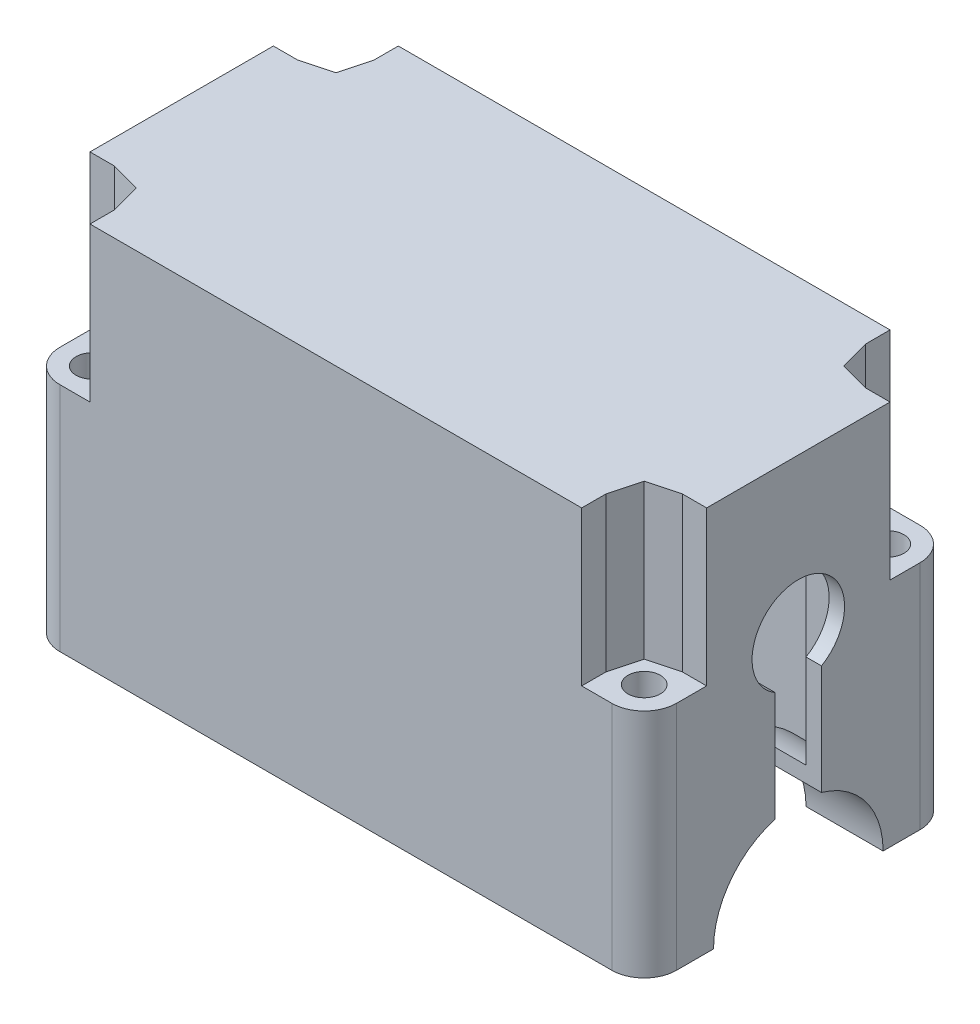
SolidWorks part; units mm, degrees
ref_plane "Front Plane" through (0, 0, 0) normal (0, 0, 1) x (1, 0, 0)
ref_plane "Top Plane" through (0, 0, 0) normal (0, 1, 0) x (1, 0, 0)
ref_plane "Right Plane" through (0, 0, 0) normal (1, 0, 0) x (0, 0, -1)
sketch "Esquisse1" plane through (0, 0, 0) normal (0, 1, 0) x (1, 0, 0)
  line L1 (0, 0) -> (80, 0)
  line L2 (0, 0) -> (0, 40)
  line L3 (0, 40) -> (80, 40)
  line L4 (80, 0) -> (80, 40)
  dimension "D1" = 40
  dimension "D2" = 80
extrude "Boss.-Extru.1" add sketch "Esquisse1" along normal blind 50
sketch "Esquisse2" plane through (0, 0, 0) normal (-1, 0, 0) x (0, 0, 1)
  line L0 (-40, 0) -> (0, 0) construction
  line L1 (-38, 48) -> (-2, 48)
  line L2 (-38, 48) -> (-38, 2)
  line L3 (-38, 2) -> (-2, 2)
  line L4 (-2, 48) -> (-2, 2)
  line L5 (-40, 50) -> (-40, 0) construction
  line L6 (-40, 50) -> (0, 50) construction
  line L7 (0, 50) -> (0, 0) construction
  circle A0 centre (-20, 0) radius 13
  dimension "D1" = 26
  dimension "D2" = 2
  dimension "D3" = 2
  dimension "D4" = 2
  dimension "D5" = 2
extrude "Enlèv. mat.-Extru.1" cut sketch "Esquisse2" against normal blind 78 contours A0 L3 L4 L1 L2
sketch "Esquisse3" plane through (0, 0, -40) normal (0, 0, -1) x (-1, 0, 0)
  line L0 (-80, 0) -> (0, 0) construction
  line L1 (0, 50) -> (-2, 50)
  line L2 (0, 50) -> (0, 0)
  line L3 (0, 0) -> (-2, 0)
  line L4 (-2, 50) -> (-2, 0)
  dimension "D1" = 2
extrude "Boss.-Extru.2" add sketch "Esquisse3" against normal blind 40
sketch "Esquisse4" plane through (0, 0, 0) normal (-1, 0, 0) x (0, 0, 1)
  line L0 (-40, 0) -> (0, 0) construction
  circle A0 centre (-20, 0) radius 11
  dimension "D1" = 22
extrude "Enlèv. mat.-Extru.2" cut sketch "Esquisse4" against normal through all
sketch "Esquisse5" plane through (0, 0, 0) normal (0, -1, 0) x (1, 0, 0)
  line L0 (80, -31) -> (80, -40) construction
  line L1 (70, -38) -> (10, -38)
  line L2 (70, -38) -> (70, -2)
  line L3 (70, -2) -> (10, -2)
  line L4 (10, -38) -> (10, -2)
  line L5 (0, -40) -> (0, -31) construction
  line L6 (80, -40) -> (0, -40) construction
  line L7 (0, 0) -> (80, 0) construction
  dimension "D1" = 10
  dimension "D2" = 10
  dimension "D3" = 2
  dimension "D4" = 2
extrude "Enlèv. mat.-Extru.3" cut sketch "Esquisse5" against normal blind 48
sketch "Esquisse6" plane through (0, 0, 0) normal (-1, 0, 0) x (0, 0, 1)
  line L0 (-40, 50) -> (0, 50) construction
  line L1 (-25, 43) -> (-15, 43)
  line L2 (-25, 43) -> (-25, 38)
  line L3 (-25, 38) -> (-15, 38)
  line L4 (-15, 43) -> (-15, 38)
  line L5 (-40, 50) -> (-40, 0) construction
  dimension "D1" = 7
  dimension "D2" = 5
  dimension "D3" = 10
  dimension "D4" = 15
extrude "Enlèv. mat.-Extru.4" cut sketch "Esquisse6" against normal blind 2
sketch "Esquisse7" plane through (80, 0, 0) normal (1, 0, 0) x (0, 0, -1)
  line L0 (40, 50) -> (40, 0) construction
  line L1 (0, 50) -> (40, 50) construction
  line L3 (17, 27.0217) -> (23, 27.0217)
  line L4 (17, 27.0217) -> (17, 7.0217)
  line L5 (17, 7.0217) -> (23, 7.0217)
  line L6 (23, 27.0217) -> (23, 7.0217)
  circle A0 centre (20, 30) radius 6
  arc M2 (9, 0) -> (31, 0) centre (20, 0) cw
  dimension "D1" = 12
  dimension "D2" = 20
  dimension "D3" = 20
  dimension "D4" = 6
  dimension "D5" = 3
  dimension "D6" = 20
extrude "Enlèv. mat.-Extru.5" cut sketch "Esquisse7" against normal blind 10 contours L4 A0 L6 L3 | L6 A0 L4 L3 | A0 L4 L6 M2
sketch "Esquisse8" plane through (0, 50, 0) normal (0, 1, 0) x (1, 0, 0)
  line L1 (0, 0) -> (10, 0)
  line L2 (0, 0) -> (0, 9)
  line L3 (0, 9) -> (10, 9)
  line L4 (10, 0) -> (10, 9)
  line L5 (0, 40) -> (10, 40)
  line L6 (0, 40) -> (0, 31)
  line L7 (0, 31) -> (10, 31)
  line L8 (10, 40) -> (10, 31)
  line L9 (80, 40) -> (70, 40)
  line L10 (80, 40) -> (80, 31)
  line L11 (80, 31) -> (70, 31)
  line L12 (70, 40) -> (70, 31)
  line L13 (80, 0) -> (70, 0)
  line L14 (80, 0) -> (80, 9)
  line L15 (80, 9) -> (70, 9)
  line L16 (70, 0) -> (70, 9)
  dimension "D1" = 10
  dimension "D2" = 9
  dimension "D3" = 9
  dimension "D4" = 10
  dimension "D5" = 10
  dimension "D6" = 9
  dimension "D7" = 9
  dimension "D8" = 10
extrude "Boss.-Extru.3" add sketch "Esquisse8" against normal blind 50
sketch "Esquisse9" plane through (0, 50, 0) normal (0, 1, 0) x (1, 0, 0)
  line L0 (80, 0) -> (80, 40) construction
  line L1 (0, 0) -> (80, 0) construction
  line L2 (0, 40) -> (0, 0) construction
  line L3 (80, 40) -> (0, 40) construction
  circle A0 centre (75.8, 4.2) radius 2.1
  circle A1 centre (4.2, 4.2) radius 2.1
  circle A2 centre (4.2, 35.8) radius 2.1
  circle A3 centre (75.8, 35.8) radius 2.1
  dimension "D1" = 4.2
  dimension "D4" = 4.2
  dimension "D9" = 4.2
  dimension "D10" = 4.2
  dimension "D11" = 4.2
  dimension "D2" = 4.2
  dimension "D3" = 4.2
  dimension "D5" = 4.2
  dimension "D6" = 4.2
  dimension "D7" = 4.2
  dimension "D8" = 4.2
  dimension "D12" = 4.2
extrude "Enlèv. mat.-Extru.6" cut sketch "Esquisse9" against normal through all
sketch "Esquisse10" plane through (0, 50, 0) normal (0, 1, 0) x (1, 0, 0)
  line L0 (8.1037, 36.846) -> (8.1037, 40)
  line L1 (5.246, 39.7037) -> (1.3423, 38.6577)
  line L2 (1.3423, 38.6577) -> (0.2963, 34.754)
  line L3 (0.2963, 34.754) -> (3.154, 31.8963)
  line L4 (3.154, 31.8963) -> (7.0577, 32.9423)
  line L5 (7.0577, 32.9423) -> (8.1037, 36.846)
  line L6 (8.1037, 36.846) -> (5.246, 39.7037)
  line L7 (72.9423, 32.9423) -> (76.846, 31.8963)
  line L8 (76.846, 31.8963) -> (79.7037, 34.754)
  line L9 (79.7037, 34.754) -> (78.6577, 38.6577)
  line L10 (78.6577, 38.6577) -> (74.754, 39.7037)
  line L11 (74.754, 39.7037) -> (71.8963, 36.846)
  line L12 (71.8963, 36.846) -> (72.9423, 32.9423)
  line L13 (74.754, 0.2963) -> (78.6577, 1.3423)
  line L14 (78.6577, 1.3423) -> (79.7037, 5.246)
  line L15 (79.7037, 5.246) -> (76.846, 8.1037)
  line L16 (76.846, 8.1037) -> (72.9423, 7.0577)
  line L17 (72.9423, 7.0577) -> (71.8963, 3.154)
  line L18 (71.8963, 3.154) -> (74.754, 0.2963)
  line L19 (5.246, 0.2963) -> (8.1037, 3.154)
  line L20 (8.1037, 3.154) -> (7.0577, 7.0577)
  line L21 (7.0577, 7.0577) -> (3.154, 8.1037)
  line L22 (3.154, 8.1037) -> (0.2963, 5.246)
  line L23 (0.2963, 5.246) -> (1.3423, 1.3423)
  line L24 (1.3423, 1.3423) -> (5.246, 0.2963)
  line L25 (80, 40) -> (0, 40) construction
  line L26 (8.1037, 40) -> (0, 40)
  line L27 (0, 40) -> (0, 31.8963)
  line L28 (0, 40) -> (0, 0) construction
  line L29 (0, 31.8963) -> (3.154, 31.8963)
  line L30 (3.154, 8.1037) -> (0, 8.1037)
  line L31 (0, 8.1037) -> (0, 0)
  line L32 (0, 0) -> (8.1037, 0)
  line L33 (0, 0) -> (80, 0) construction
  line L34 (8.1037, 0) -> (8.1037, 3.154)
  line L35 (71.8963, 3.154) -> (71.8963, 0)
  line L36 (71.8963, 0) -> (80, 0)
  line L37 (80, 0) -> (80, 8.1037)
  line L38 (80, 0) -> (80, 40) construction
  line L39 (80, 8.1037) -> (76.846, 8.1037)
  line L40 (76.846, 31.8963) -> (80, 31.8963)
  line L41 (80, 31.8963) -> (80, 40)
  line L42 (80, 40) -> (71.8963, 40)
  line L43 (71.8963, 40) -> (71.8963, 36.846)
  circle A0 centre (4.2, 35.8) radius 3.5 construction
  circle A1 centre (75.8, 35.8) radius 3.5 construction
  circle A2 centre (75.8, 4.2) radius 3.5 construction
  circle A3 centre (4.2, 4.2) radius 3.5 construction
  circle M1 centre (75.8, 35.8) radius 2.1
  circle M2 centre (4.2, 35.8) radius 2.1
  circle M3 centre (4.2, 4.2) radius 2.1
  circle M4 centre (75.8, 4.2) radius 2.1
  line M5 (0, 0) -> (80, 0)
  line M6 (80, 0) -> (80, 40)
  line M7 (80, 40) -> (0, 40)
  line M8 (0, 40) -> (0, 0)
  dimension "D1" = 7
  dimension "D2" = 7
  dimension "D3" = 7
  dimension "D4" = 7
extrude "Enlèv. mat.-Extru.7" cut sketch "Esquisse10" against normal blind 20 contours L29 L3 L2 L1 L6 L0 M8 M7 | L5 L6 L1 L2 L3 L4 M2 | L23 L24 L19 L20 L21 L22 M3 | L34 L19 L24 L23 L22 L30 M5 M8 | L39 L15 L14 L13 L18 L35 M6 M5 | L17 L18 L13 L14 L15 L16 M4 | L43 L11 L10 L9 L8 L40 M7 M6 | L11 L12 L7 L8 L9 L10 M1
fillet "Congé1" radius 4.2 4 edges at (80, 15, -40) (80, 15, 0) (0, 15, -40) (0, 15, 0)
sketch "Esquisse11" plane through (0, 48, 0) normal (0, -1, 0) x (1, 0, 0)
  line L1 (2, -31) -> (2, -9) construction
  line L2 (40, -31) -> (47, -31)
  line L3 (40, -31) -> (40, -29)
  line L4 (40, -29) -> (47, -29)
  line L5 (47, -31) -> (47, -29)
  line L6 (45, -29) -> (47, -29)
  line L7 (45, -29) -> (45, -24)
  line L8 (45, -24) -> (47, -24)
  line L9 (47, -29) -> (47, -24)
  line L10 (45, -16) -> (47, -16)
  line L11 (45, -16) -> (45, -11)
  line L12 (45, -11) -> (47, -11)
  line L13 (47, -16) -> (47, -11)
  line L14 (47, -11) -> (40, -11)
  line L15 (47, -11) -> (47, -9)
  line L16 (47, -9) -> (40, -9)
  line L18 (40, -11) -> (40, -9)
  point P20 (2, -20)
  dimension "D1" = 18
  dimension "D2" = 5
  dimension "D3" = 5
  dimension "D4" = 7
  dimension "D5" = 7
  dimension "D6" = 2
  dimension "D7" = 2
  dimension "D8" = 2
  dimension "D9" = 2
  dimension "D10" = 43
  dimension "D11" = 9
  dimension "D12" = 43
extrude "Boss.-Extru.4" add sketch "Esquisse11" along normal blind 5 contours L10 L13 L12 L11 | L18 L14 L12 L15 L16 | L4 L9 L8 L7 | L2 L5 L4 L3
